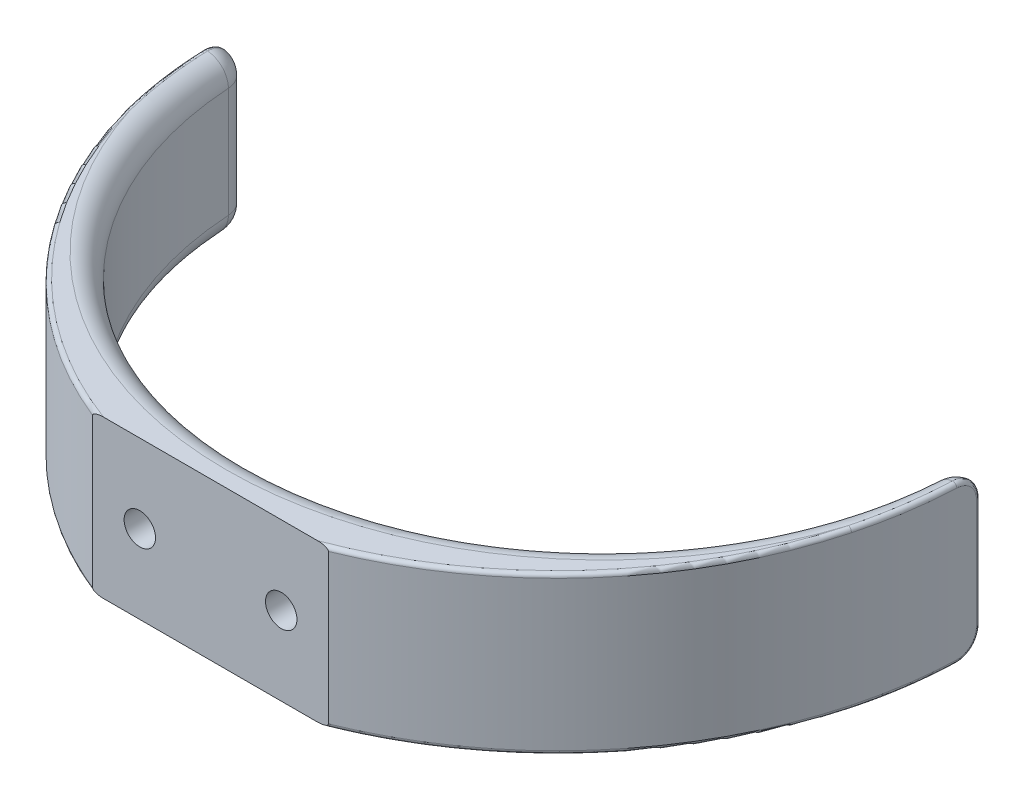
SolidWorks part; units mm, degrees
ref_plane "Front Plane" through (0, 0, 0) normal (0, 0, 1) x (1, 0, 0)
ref_plane "Top Plane" through (0, 0, 0) normal (0, 1, 0) x (1, 0, 0)
ref_plane "Right Plane" through (0, 0, 0) normal (1, 0, 0) x (0, 0, -1)
sketch "Sketch1" plane through (0, 0, 0) normal (0, 1, 0) x (1, 0, 0)
  line L0 (0, 0) -> (15, 0)
  line L1 (48, 50) -> (45, 50)
  line L2 (0, 5) -> (0, 0)
  line L4 (31.8198, 18.1802) -> (35.3553, 14.6447) construction
  arc A1 (45, 50) -> (0, 5) centre (0, 50) cw
  arc A2 (48, 50) -> (15, 0) centre (-4.7565, 48.9293) cw
  point P10 (0, 0)
  dimension "D3" = 45
  dimension "D1" = 15
  dimension "D2" = 5
  dimension "D4" = 3
  dimension "D5" = 45
  dimension "D6" = 5
extrude "Boss-Extrude1" add sketch "Sketch1" along normal blind 20 contours A1 L2 L0 A2 L1
mirror "Mirror1" about plane through (0, 20, -5) normal (1, 0, 0) of bodies 101
sketch "Sketch2" plane through (0, 0, 0) normal (0, 0, 1) x (1, 0, 0)
  line L0 (-9, 10) -> (9, 10) construction
  line L3 (-15, 20) -> (15, 20) construction
  line L4 (-15, 0) -> (15, 0) construction
  line L5 (0, 0) -> (0, 20) construction
  circle A0 centre (-9, 10) radius 2
  circle A1 centre (9, 10) radius 2
  point P10 (0, 0)
  point P11 (0, 10)
  dimension "D2" = 4
  dimension "D1" = 18
extrude "Cut-Extrude1" cut sketch "Sketch2" against normal through all
sketch "Sketch3" plane through (0, 0, 0) normal (0, 0, 1) x (1, 0, 0)
  circle A16 centre (-9, 10) radius 4
  circle A17 centre (9, 10) radius 4
  dimension "D1" = 8
  dimension "D2" = 8
extrude "Cut-Extrude2" cut sketch "Sketch3" against normal through all from offset 3 offset against normal yes
fillet "Fillet1" radius 3 5 edges at (45, 10, -50) (-46.5, 20, -50) (-45, 10, -50) (0, 0, -5) (0, 20, -5)
fillet "Fillet2" radius 3 4 edges at (47.9531, 0.0004, -50) (47.9531, 19.9996, -50) (-47.9531, 19.9996, -50) (-47.9531, 0.0004, -50)
fillet "Fillet3" radius 0.5 12 edges at (38.4396, 20, -18.6226) (48.0092, 18.874, -49.3427) (48, 10, -50) (48.0108, 0.6558, -48.8721) (-38.4396, 20, -18.6226) (-48.0108, 19.3442, -48.8721) (-48, 10, -50) (-48.0092, 1.126, -49.3427) (38.4396, 0, -18.6226) (-38.4396, 0, -18.6226) (-12.894, 9.0851, -6.8868) (5.0973, 9.1233, -5.2896)
